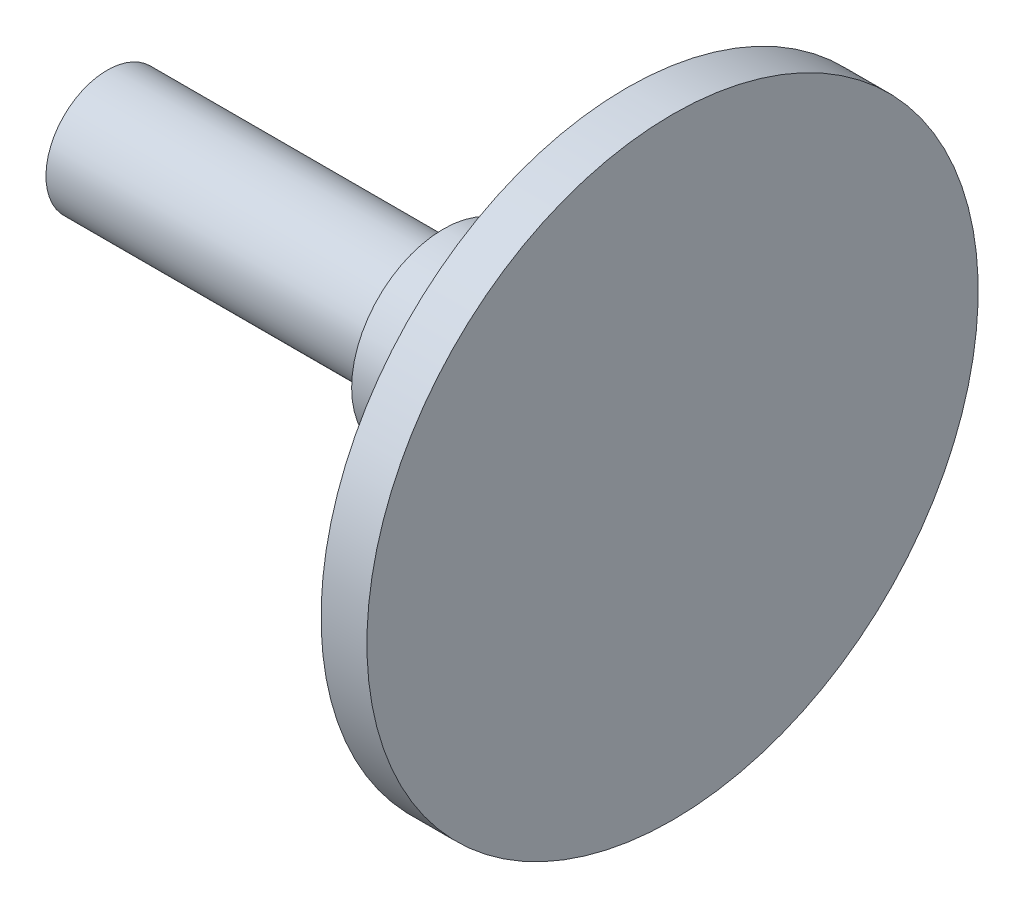
SolidWorks part; units mm, degrees
material "普通碳钢"
ref_plane "前视基准面" through (0, 0, 0) normal (0, 0, 1) x (1, 0, 0)
ref_plane "上视基准面" through (0, 0, 0) normal (0, 1, 0) x (1, 0, 0)
ref_plane "右视基准面" through (0, 0, 0) normal (1, 0, 0) x (0, 0, -1)
sketch "草图1" plane through (0, 0, 0) normal (0, 0, 1) x (1, 0, 0)
  line L0 (-18.5, 0) -> (62.2475, 0) construction
  line L1 (-18.5, 0) -> (-18.5, 2)
  line L2 (-18.5, 2) -> (-1.5, 2)
  line L5 (-1.5, 2) -> (-1.5, 10)
  line L6 (-1.5, 10) -> (0, 10)
  line L7 (0, 10) -> (0, 2)
  line L9 (0, 2) -> (0, 0)
  line L10 (-18.5, 0) -> (0, 0)
  dimension "D1" = 17
  dimension "D3" = 1.5
  dimension "D5" = 2
  dimension "D7" = 10
revolve "旋转1" add sketch "草图1" angle 360 about L0
sketch "草图2" plane through (-1.5, 0, 0) normal (-1, 0, 0) x (0, 0, 1)
  circle A0 centre (0, 0) radius 3
extrude "凸台-拉伸1" add sketch "草图2" along normal blind 6
